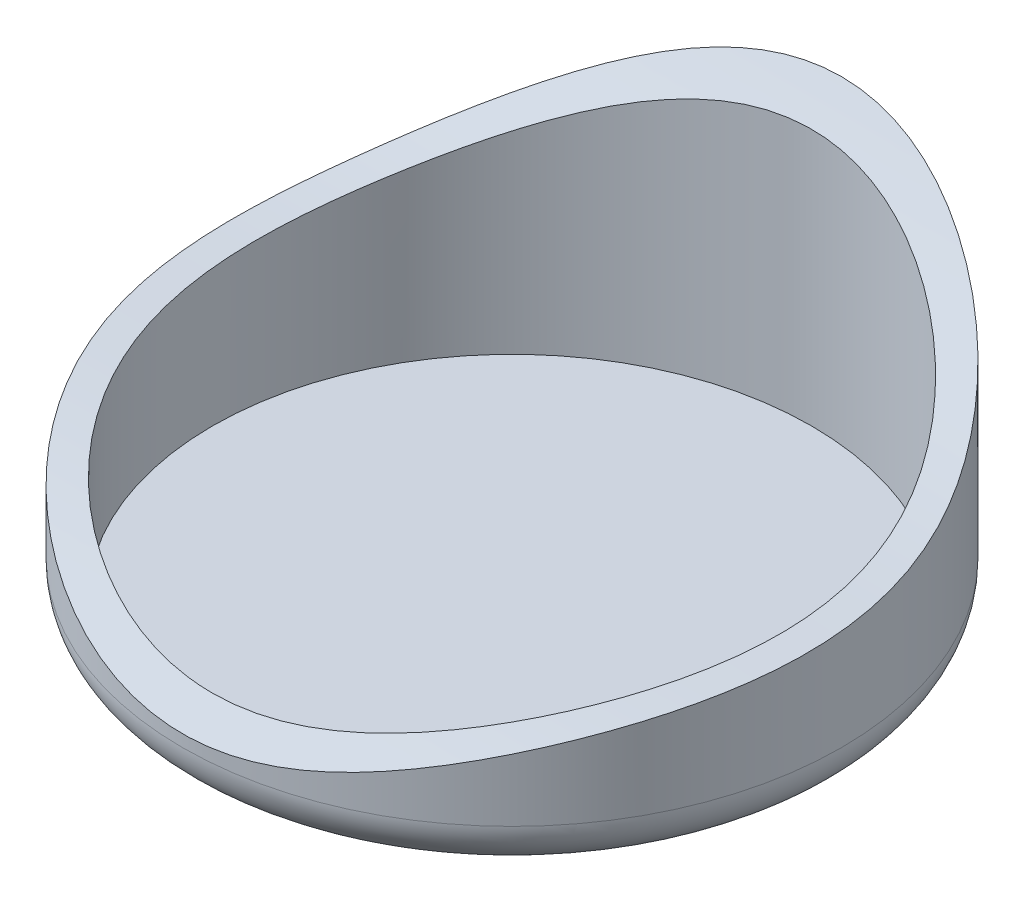
SolidWorks part; units mm, degrees
ref_plane "Front Plane" through (0, 0, 0) normal (0, 0, 1) x (1, 0, 0)
ref_plane "Top Plane" through (0, 0, 0) normal (0, 1, 0) x (1, 0, 0)
ref_plane "Right Plane" through (0, 0, 0) normal (1, 0, 0) x (0, 0, -1)
sketch "Sketch1" plane through (0, 0, 0) normal (0, 1, 0) x (1, 0, 0)
  circle A0 centre (0, 0) radius 55
  dimension "D1" = 110
extrude "Boss-Extrude1" add sketch "Sketch1" along normal blind 50
sketch "Sketch2" plane through (0, 50, 0) normal (0, 1, 0) x (1, 0, 0)
  circle A0 centre (0, 0) radius 50
  dimension "D1" = 100
extrude "Cut-Extrude1" cut sketch "Sketch2" against normal blind 48
sketch "Sketch3" plane through (0, 0, 0) normal (1, 0, 0) x (0, 0, -1)
  line L0 (-55, 0) -> (-55, 10) construction
  line L1 (-55, 10) -> (-55, 50)
  line L2 (-55, 50) -> (55, 50)
  spline S0 degree 3 poles (-55, 10) (-32.1856, 27.4053) (13.1907, 18.203) (46.2899, 40.2896) (55, 50) knots 0 0 0 0 0.690633 1 1 1 1
  dimension "D1" = 10
extrude "Cut-Extrude2" cut sketch "Sketch3" against normal mid plane 128 contours L2 S0 L1
sketch "Sketch4" plane through (0, 0, 0) normal (0, -1, 0) x (1, 0, 0)
  circle A0 centre (0, 0) radius 45
  dimension "D1" = 90
extrude "Boss-Extrude2" add sketch "Sketch4" along normal blind 2
fillet "Fillet1" radius 8 1 edges at (0, 0, 55)
